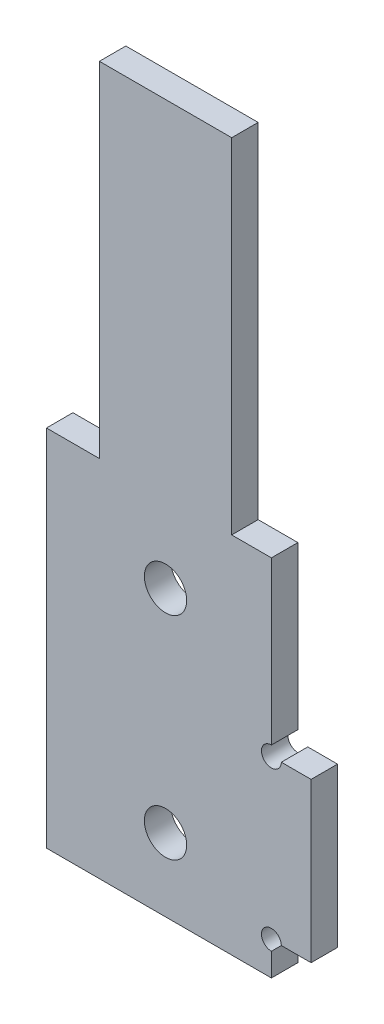
SolidWorks part; units mm, degrees
material "Thornel Mat VMA"
ref_plane "前视基准面" through (0, 0, 0) normal (0, 0, 1) x (1, 0, 0)
ref_plane "上视基准面" through (0, 0, 0) normal (0, 1, 0) x (1, 0, 0)
ref_plane "右视基准面" through (0, 0, 0) normal (1, 0, 0) x (0, 0, -1)
sketch "草图1" plane through (0, 0, 0) normal (0, 0, 1) x (1, 0, 0)
  line L1 (0, 0) -> (17, 0)
  line L2 (0, 0) -> (0, 51.5)
  line L3 (0, 51.5) -> (17, 51.5)
  line L4 (20, 2.5) -> (20, 14.5)
  line L7 (20, 2.5) -> (17, 2.5)
  line L8 (17, 0) -> (17, 2.5)
  line L11 (20, 14.5) -> (17, 14.5)
  line L12 (17, 51.5) -> (17, 14.5)
  point P11 (18.5, 2.5)
  dimension "D1" = 51.5
  dimension "D2" = 17
  dimension "D3" = 17
  dimension "D4" = 2.5
  dimension "D5" = 12
  dimension "D6" = 3
extrude "凸台-拉伸1" add sketch "草图1" along normal blind 2
sketch "草图2" plane through (0, 0, 2) normal (0, 0, 1) x (1, 0, 0)
  line L0 (0, 0) -> (17, 0) construction
  line L1 (0, 51.5) -> (0, 0) construction
  circle A0 centre (9, 5.5) radius 1.6
  circle A1 centre (9, 21.5) radius 1.6
  dimension "D1" = 3.2
  dimension "D2" = 3.2
  dimension "D3" = 5.5
  dimension "D4" = 9
  dimension "D5" = 16
  dimension "D6" = 9
extrude "切除-拉伸1" cut sketch "草图2" against normal through all
sketch "草图3" plane through (0, 0, 2) normal (0, 0, 1) x (1, 0, 0)
  line L0 (0, 0) -> (17, 0) construction
  line L1 (17, 51.5) -> (14, 51.5)
  line L2 (17, 51.5) -> (17, 27.5)
  line L3 (17, 27.5) -> (14, 27.5)
  line L4 (14, 51.5) -> (14, 27.5)
  line L6 (0, 51.5) -> (4, 51.5)
  line L7 (0, 51.5) -> (0, 27.5)
  line L8 (0, 27.5) -> (4, 27.5)
  line L9 (4, 51.5) -> (4, 27.5)
  dimension "D1" = 27.5
  dimension "D2" = 3
  dimension "D3" = 4
extrude "切除-拉伸2" cut sketch "草图3" against normal through all
sketch "草图4" plane through (0, 51.5, 0) normal (0, 1, 0) x (1, 0, 0)
  line L1 (4, 0) -> (14, 0)
  line L2 (4, 0) -> (4, -2)
  line L3 (4, -2) -> (14, -2)
  line L4 (14, 0) -> (14, -2)
extrude "凸台-拉伸2" add sketch "草图4" along normal blind 2
sketch "草图5" plane through (0, 0, 2) normal (0, 0, 1) x (1, 0, 0)
  circle A0 centre (17, 14.5) radius 0.75
  circle A1 centre (17, 2.5) radius 0.75
  dimension "D1" = 1.5
  dimension "D2" = 1.5
extrude "切除-拉伸3" cut sketch "草图5" against normal blind 3
